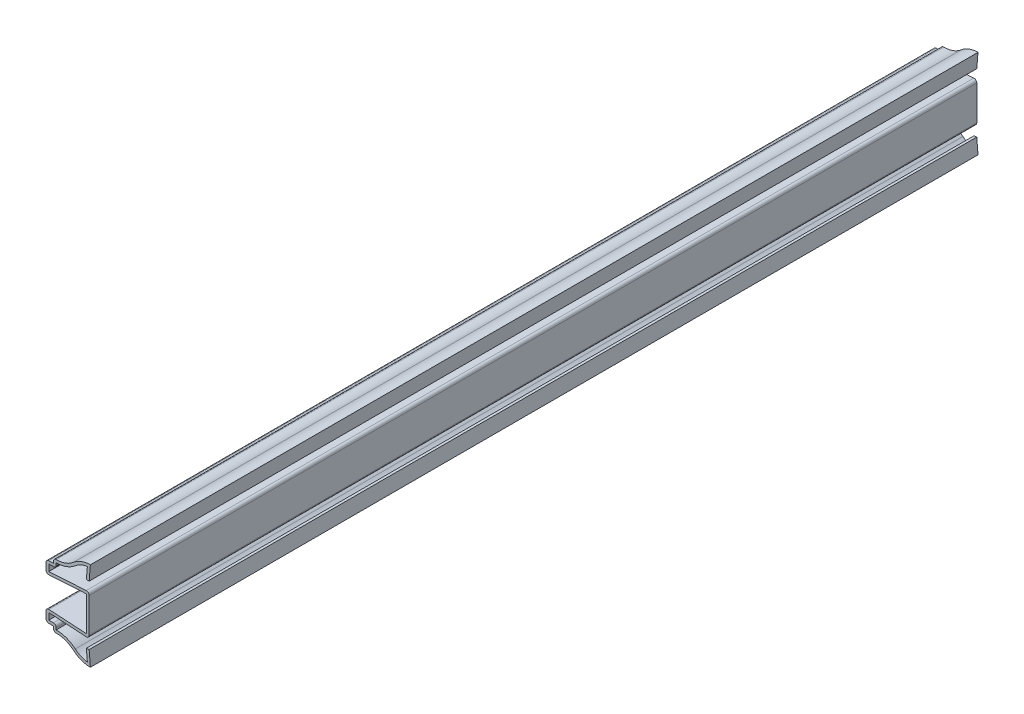
SolidWorks part; units mm, degrees
ref_plane "Front Plane" through (0, 0, 0) normal (0, 0, 1) x (1, 0, 0)
ref_plane "Top Plane" through (0, 0, 0) normal (0, 1, 0) x (1, 0, 0)
ref_plane "Right Plane" through (0, 0, 0) normal (1, 0, 0) x (0, 0, -1)
sketch "Sketch1" plane through (0, 0, 0) normal (0, 0, 1) x (1, 0, 0)
  line L0 (0, 0) -> (-10.6042, 0) construction
  line L1 (-1.2859, -5.5562) -> (-1.2859, 5.5562)
  line L2 (-1.2859, 5.5562) -> (-14.2875, 4.7625)
  line L3 (-14.2875, 4.7625) -> (-14.2875, 8.7313)
  line L4 (-14.2875, 8.7313) -> (-11.9062, 8.7313)
  line L5 (-11.9062, 8.7313) -> (-11.9062, 10.3188)
  line L6 (0, 14.2875) -> (-0.3969, 9.525)
  line L7 (-11.9062, -8.7313) -> (-11.9062, -10.3188)
  line L8 (-14.2875, -8.7313) -> (-11.9062, -8.7313)
  line L9 (-14.2875, -4.7625) -> (-14.2875, -8.7313)
  line L10 (-1.2859, -5.5562) -> (-14.2875, -4.7625)
  line L11 (0, -14.2875) -> (-0.3969, -9.525)
  arc A0 (-11.9062, 10.3188) -> (-5.4358, 12.2709) centre (-10.8716, 18.5886) ccw
  arc A1 (-5.4358, 12.2709) -> (0, 14.2875) centre (0, 5.9531) cw
  arc A2 (-5.4358, -12.2709) -> (0, -14.2875) centre (0, -5.9531) ccw
  arc A3 (-11.9062, -10.3188) -> (-5.4358, -12.2709) centre (-10.8716, -18.5886) cw
  point P13 (0, 0)
  point P15 (0, 0)
  point P16 (0, 0)
  point P30 (-1.2859, 0)
  dimension "D11" = 8.3344
  dimension "D1" = 28.575
  dimension "D2" = 14.2875
  dimension "D3" = 1.2859
  dimension "D4" = 0.3969
  dimension "D5" = 3.9688
  dimension "D6" = 1.5875
  dimension "D7" = 3.9688
  dimension "D8" = 11.1125
  dimension "D9" = 2.3813
  dimension "D10" = 4.7625
extrude "Extrude-Thin1" add sketch "Sketch1" against normal blind 285.75 thin
fillet "Fillet1" radius 0.889 10 edges at (-11.9062, -10.3188, -142.875) (-11.0172, -7.8423, -142.875) (-14.2875, -8.7313, -142.875) (-14.2875, -4.7625, -142.875) (-0.3969, -6.5012, -142.875) (-0.3969, 6.5012, -142.875) (-14.2875, 4.7625, -142.875) (-14.2875, 8.7313, -142.875) (-11.0172, 7.8423, -142.875) (-11.9062, 10.3188, -142.875)
